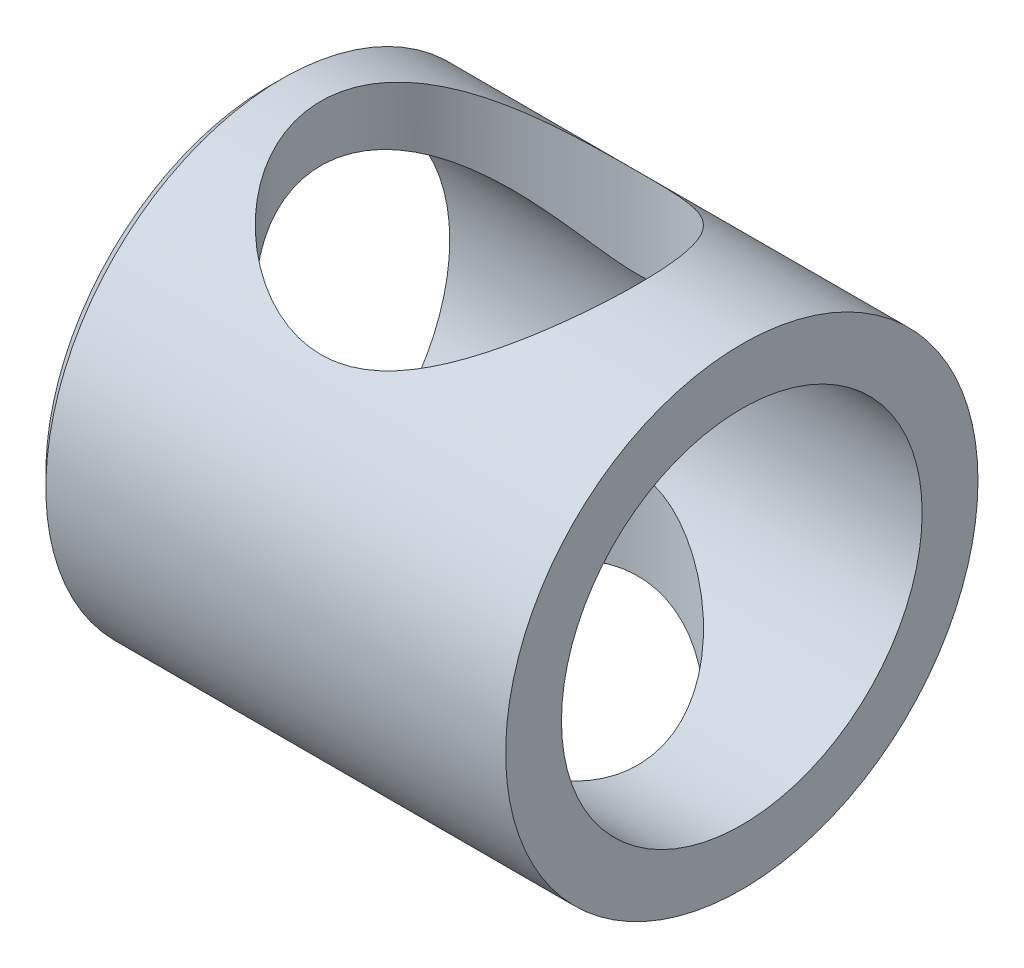
SolidWorks part; units mm, degrees
ref_plane "Front Plane" through (0, 0, 0) normal (0, 0, 1) x (1, 0, 0)
ref_plane "Top Plane" through (0, 0, 0) normal (0, 1, 0) x (1, 0, 0)
ref_plane "Right Plane" through (0, 0, 0) normal (1, 0, 0) x (0, 0, -1)
sketch "Sketch1" plane through (0, 0, 0) normal (1, 0, 0) x (0, 0, -1)
  circle A0 centre (0, 0) radius 10.9093
  circle A1 centre (0, 0) radius 14.2875
  dimension "D1" = 21.8186
  dimension "D2" = 28.575
extrude "Boss-Extrude1" add sketch "Sketch1" along normal blind 28.575
sketch "Sketch2" plane through (0, 0, 0) normal (0, 1, 0) x (1, 0, 0)
  line L0 (0, 0) -> (12.7, 0) construction
  circle A0 centre (12.7, 0) radius 9.5885
  dimension "D1" = 19.177
  dimension "D2" = 12.7
extrude "Cut-Extrude1" cut sketch "Sketch2" against normal mid plane 38.1
chamfer "Chamfer1" distance 0.762 angle 45 1 edges at (0, 0, -14.2875)
ref_point "Point1"
